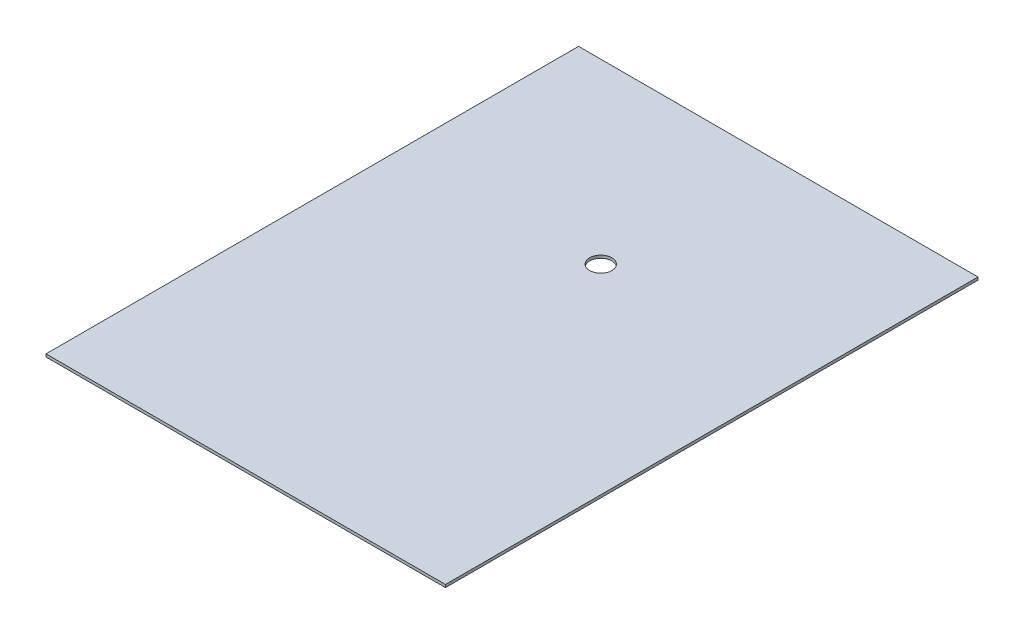
SolidWorks part; units mm, degrees
ref_plane "Front" through (0, 0, 0) normal (0, 0, 1) x (1, 0, 0)
ref_plane "Top" through (0, 0, 0) normal (0, 1, 0) x (1, 0, 0)
ref_plane "Right" through (0, 0, 0) normal (1, 0, 0) x (0, 0, -1)
sketch "Sketch1" plane through (0, 0, 0) normal (0, 1, 0) x (1, 0, 0)
  line L0 (0, 304.8) -> (0, -304.8) construction
  line L1 (-228.6, 304.8) -> (228.6, 304.8)
  line L2 (-228.6, 304.8) -> (-228.6, -304.8)
  line L3 (-228.6, -304.8) -> (228.6, -304.8)
  line L4 (228.6, 304.8) -> (228.6, -304.8)
  circle A0 centre (0, 101.6) radius 12.7
  point P6 (0, 0)
  dimension "D3" = 25.4
  dimension "D1" = 457.2
  dimension "D2" = 609.6
  dimension "D4" = 406.4
extrude "Boss-Extrude1" add sketch "Sketch1" along normal blind 3.175
